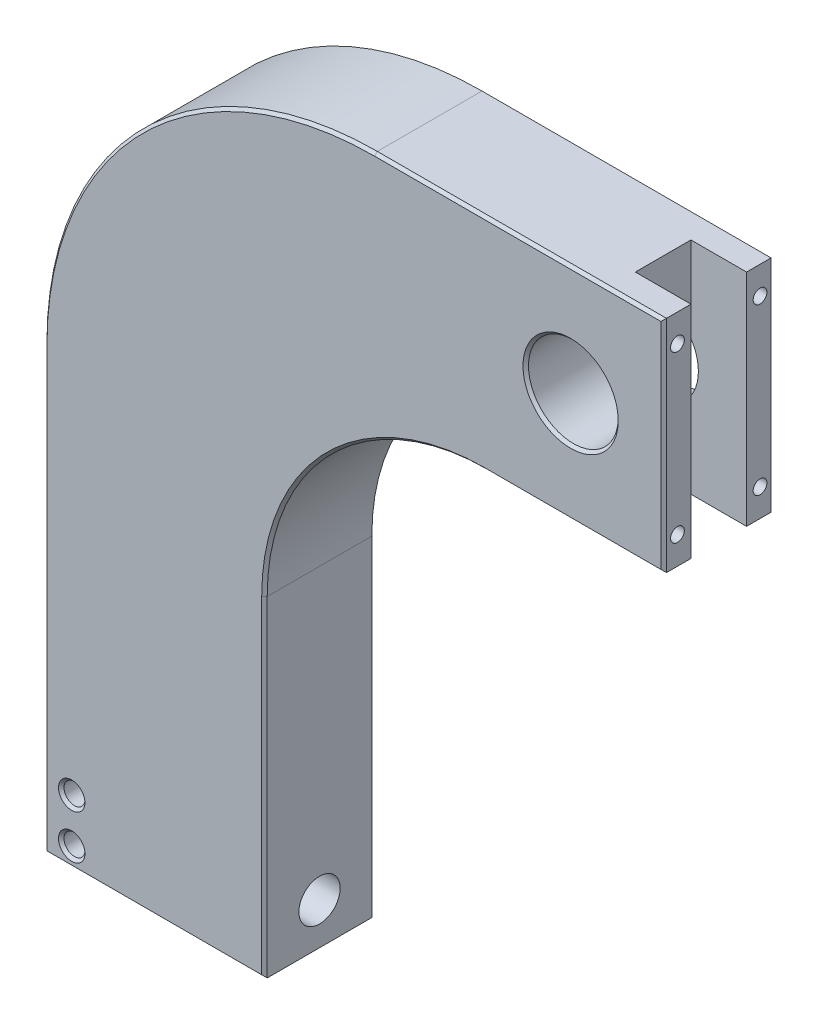
SolidWorks part; units mm, degrees
ref_plane "Front Plane" through (0, 0, 0) normal (0, 0, 1) x (1, 0, 0)
ref_plane "Top Plane" through (0, 0, 0) normal (0, 1, 0) x (1, 0, 0)
ref_plane "Right Plane" through (0, 0, 0) normal (1, 0, 0) x (0, 0, -1)
sketch "Sketch1" plane through (0, 0, 0) normal (0, 0, 1) x (1, 0, 0)
  line L0 (0, 0) -> (0, 8)
  line L1 (6, 14) -> (11.25, 14)
  line L2 (11.25, 14) -> (11.25, 10)
  line L3 (11.25, 10) -> (8, 10)
  line L4 (4, 6) -> (4, 0)
  line L5 (4, 0) -> (0, 0)
  arc A0 (0, 8) -> (6, 14) centre (6, 8) cw
  arc A1 (8, 10) -> (4, 6) centre (8, 6) ccw
  circle A2 centre (0.5, 0.35) radius 0.19
  circle A3 centre (0.5, 1.15) radius 0.19
  circle A4 centre (9.56, 12) radius 0.815
  point P9 (0, 14)
  point P18 (11.25, 12)
  dimension "D5" = 6
  dimension "D6" = 4
  dimension "D9" = 0.38
  dimension "D14" = 1.63
  dimension "D1" = 14
  dimension "D2" = 11.25
  dimension "D3" = 4
  dimension "D4" = 4
  dimension "D7" = 0.35
  dimension "D8" = 1.15
  dimension "D10" = 0.5
  dimension "D11" = 0.5
  dimension "D12" = 3.5
  dimension "D13" = 1.69
  dimension "D15" = 1.69
extrude "Boss-Extrude1" add sketch "Sketch1" along normal mid plane 2
sketch "Sketch2" plane through (4, 0, 0) normal (1, 0, 0) x (0, 0, -1)
  line L0 (-1, 0) -> (1, 0) construction
  line L1 (1, 0) -> (1, 6) construction
  circle A0 centre (0, 0.75) radius 0.375
  dimension "D1" = 0.75
  dimension "D3" = 0.75
  dimension "D2" = 0.75
  dimension "D4" = 1
extrude "Cut-Extrude1" cut sketch "Sketch2" against normal blind 0.75
sketch "Sketch3" plane through (0, 14, 0) normal (0, 1, 0) x (1, 0, 0)
  line L0 (11.25, -1) -> (11.25, 1) construction
  line L1 (11.25, 0.505) -> (10.24, 0.505)
  line L2 (11.25, 0.505) -> (11.25, -0.505)
  line L3 (11.25, -0.505) -> (10.24, -0.505)
  line L4 (10.24, 0.505) -> (10.24, -0.505)
  line L5 (11.25, 0) -> (9.4354, 0) construction
  point P9 (10.24, 0)
  dimension "D1" = 1.01
  dimension "D2" = 1.01
extrude "Cut-Extrude2" cut sketch "Sketch3" against normal through all
sketch "Sketch4" plane through (11.25, 0, 0) normal (1, 0, 0) x (0, 0, -1)
  line L0 (-1, 10) -> (-0.505, 10) construction
  line L1 (-1, 10) -> (-1, 14) construction
  line L2 (0.505, 14) -> (1, 14) construction
  line L3 (-1, 14) -> (-0.505, 14) construction
  line L5 (1, 10) -> (1, 14) construction
  line L6 (0.505, 10) -> (1, 10) construction
  circle A0 centre (0.75, 13.5) radius 0.125
  circle A1 centre (0.75, 10.5) radius 0.125
  circle A2 centre (-0.75, 10.5) radius 0.125
  circle A3 centre (-0.75, 13.5) radius 0.125
  dimension "D1" = 0.25
  dimension "D2" = 0.25
  dimension "D3" = 0.25
  dimension "D4" = 0.5
  dimension "D5" = 0.5
  dimension "D6" = 0.25
  dimension "D7" = 0.5
  dimension "D8" = 0.5
  dimension "D9" = 0.25
extrude "Cut-Extrude3" cut sketch "Sketch4" against normal blind 1.01
chamfer "Chamfer1" distance 0.05 angle 45 22 edges at (10.375, 12, -1) (0.69, 0.35, -1) (4, 3, -1) (5.1716, 8.8284, -1) (9.625, 10, -1) (11.25, 12, -1) (8.625, 14, -1) (1.7574, 12.2426, -1) (0, 4, -1) (2, 0, -1) (0.69, 1.15, -1) (10.375, 12, 1) (0.69, 1.15, 1) (0.69, 0.35, 1) (0, 4, 1) (1.7574, 12.2426, 1) (8.625, 14, 1) (11.25, 12, 1) (9.625, 10, 1) (5.1716, 8.8284, 1) (4, 3, 1) (2, 0, 1)
